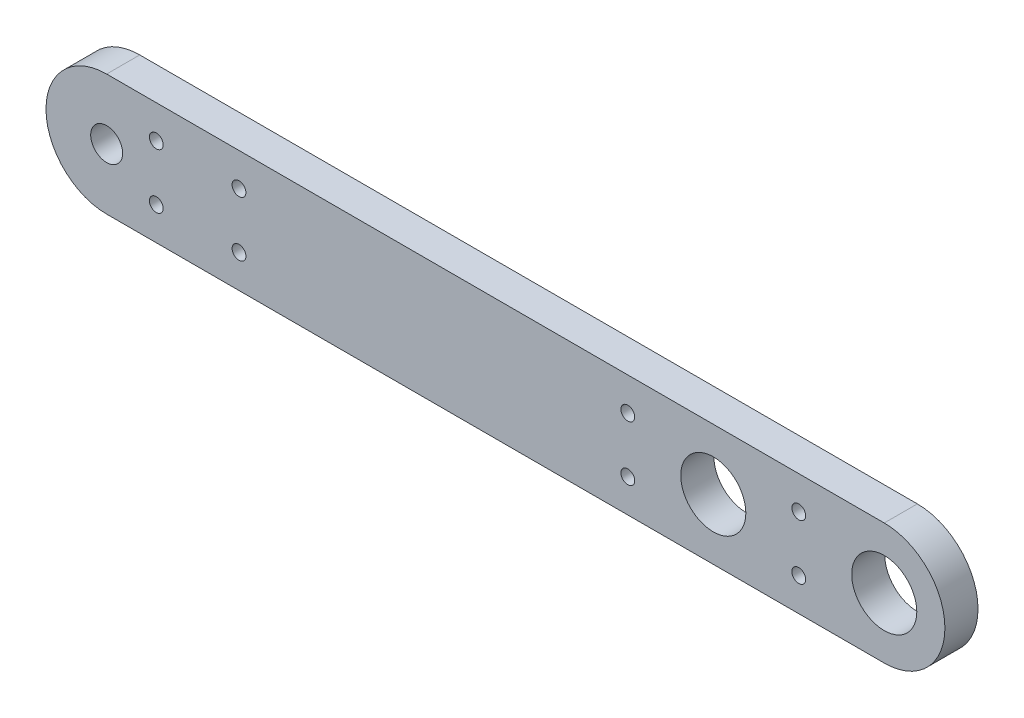
SolidWorks part; units mm, degrees
material "POM copolymère d'acétal"
ref_plane "Front Plane" through (0, 0, 0) normal (0, 0, 1) x (1, 0, 0)
ref_plane "Top Plane" through (0, 0, 0) normal (0, 1, 0) x (1, 0, 0)
ref_plane "Right Plane" through (0, 0, 0) normal (1, 0, 0) x (0, 0, -1)
sketch "Sketch1" plane through (0, 0, 0) normal (0, 0, 1) x (1, 0, 0)
  line L0 (15.5, 5.5) -> (-55, 5.5)
  line L1 (-55, -5.5) -> (15.5, -5.5)
  line L2 (0, 0) -> (31.9738, 0) construction
  arc A0 (-55, 5.5) -> (-55, -5.5) centre (-55, 0) ccw
  arc A1 (15.5, -5.5) -> (15.5, 5.5) centre (15.5, 0) ccw
  circle A2 centre (-55, 0) radius 1.45
  circle A3 centre (0, 0) radius 2.95
  circle A4 centre (15.5, 0) radius 2.95
  dimension "D1" = 5.9
  dimension "D2" = 15.5
  dimension "D3" = 2.9
  dimension "D4" = 55
  dimension "D5" = 5.5
extrude "Boss-Extrude1" add sketch "Sketch1" along normal blind 3
hole_wizard "Trou taraudé M1.61" positions "Sketch3" profile "Sketch2" tap size "M1.6" standard "Iso" end condition through all
sketch "Sketch3" plane through (0, 0, 3) normal (0, 0, 1) x (1, 0, 0)
  line L0 (0, 0) -> (-68.8863, 0) construction
  line L2 (7.75, -12.0598) -> (7.75, 13.3437) construction
  line L4 (0, 0) -> (0, 9.9697) construction
  circle A0 centre (-55, 0) radius 1.45 construction
  circle A1 centre (0, 0) radius 2.95 construction
  circle A2 centre (15.5, 0) radius 2.95 construction
  point P1 (7.75, 2.5)
  point P5 (-7.75, 2.5)
  point P7 (-50.5, 2.5)
  point P11 (-43, 2.5)
  dimension "D1" = 4.5
  dimension "D2" = 12
  dimension "D3" = 5
sketch "Sketch2" plane through (7.75, 2.5, 3) normal (1, 0, 0) x (0, -1, 0)
  line L0 (0, 0) -> (0, 3)
  line L1 (0, 3) -> (0.625, 3)
  line L2 (0.625, 3) -> (0.625, 0)
  line L5 (0.625, 0) -> (0, 0)
  line L11 (0, -6.35) -> (0, 107.95) construction
  dimension "Diamètre principal du filetage" = 1.25
  dimension "Profondeur du trou pour taraudage jusqu'au prochain" = 3
mirror "Mirror1" about plane through (0, 0, 0) normal (0, 1, 0) of "Trou taraudé M1.61"
